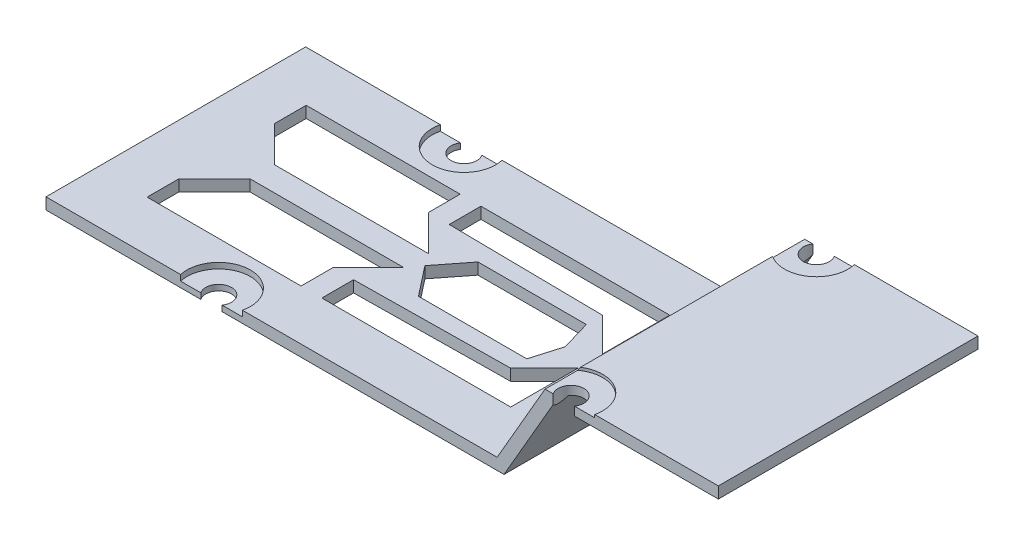
SolidWorks part; units mm, degrees
material "ABS"
ref_plane "Ön Düzlem" through (0, 0, 0) normal (0, 0, 1) x (1, 0, 0)
ref_plane "Üst Düzlem" through (0, 0, 0) normal (0, 1, 0) x (1, 0, 0)
ref_plane "Sağ Düzlem" through (0, 0, 0) normal (1, 0, 0) x (0, 0, -1)
sketch "Sketch1" plane through (0, 0, 0) normal (0, 0, 1) x (1, 0, 0)
  line L0 (-73.1543, 0) -> (-73.1543, -2)
  line L1 (44.3457, 14.9996) -> (14.3457, 14.9996)
  line L2 (14.3457, 14.9996) -> (5.6857, 0)
  line L3 (5.6857, 0) -> (-73.1543, 0)
  line L4 (-73.1543, -2) -> (6.8899, -2)
  line L5 (44.3457, 14.9996) -> (44.3457, 12.9996)
  line L6 (44.3457, 12.9996) -> (15.5499, 12.9996)
  line L7 (15.5499, 12.9996) -> (6.8899, -2)
  dimension "D1" = 120
  dimension "D2" = 17.32
  dimension "D3" = 30
  dimension "D4" = 117.5
extrude "Boss-Extrude1" add sketch "Sketch1" along normal blind 45.38
sketch "Sketch2" plane through (0, 0, 0) normal (0, 1, 0) x (1, 0, 0)
  circle A1 centre (-44.2343, -44.13) radius 2.25
ref_plane "Plane1" through (0, 0, 22.69) normal (0, 0, -1) x (-1, 0, 0)
sketch "Sketch4" plane through (0, 14.9996, 0) normal (0, 1, 0) x (1, 0, 0)
  line L0 (44.3457, -45.38) -> (17.3457, -45.38)
  line L1 (44.3457, -45.38) -> (14.3457, -45.38) construction
  line L2 (17.3457, -45.38) -> (17.3457, -44.13)
  circle A0 centre (17.3457, -44.13) radius 2.25
extrude "Cut-Extrude3" cut sketch "Sketch4" against normal up to next (14.9996 mm away) contours A0
sketch "Sketch5" plane through (0, 14.9996, 0) normal (0, 1, 0) x (1, 0, 0)
  circle A0 centre (17.3457, -44.13) radius 5.54
extrude "Cut-Extrude4" cut sketch "Sketch5" against normal blind 0.5
sketch "Sketch6" plane through (0, 0, 0) normal (0, 1, 0) x (1, 0, 0)
  line L0 (49.8222, -22.69) -> (-95.678, -22.69) construction
  line L1 (9.3498, -22.69) -> (-9.3498, -22.69) construction
  line L2 (-0.7343, -36.59) -> (-0.7343, -24.8244)
  line L3 (-33.7343, -36.59) -> (-0.7343, -36.59)
  line L4 (-0.7343, -24.8244) -> (-6.6171, -30.7072)
  line L5 (-6.6171, -30.7072) -> (-33.7343, -31.0537)
  line L6 (-33.7343, -31.0537) -> (-33.7343, -36.59)
  line L7 (-37.3689, -36.59) -> (-37.3689, -31.0537)
  line L8 (-37.3689, -31.0537) -> (-31.1395, -24.8244)
  line L9 (-31.1395, -24.8244) -> (-58.0417, -24.8244)
  line L10 (-58.0417, -24.8244) -> (-64.2711, -31.0537)
  line L11 (-64.2711, -31.0537) -> (-64.2711, -36.59)
  line L12 (-64.2711, -36.59) -> (-37.3689, -36.59)
  dimension "D1" = 33
extrude "Cut-Extrude5" cut sketch "Sketch6" against normal up to surface (2 mm away) up to face at (-33.1322, -2, 22.69)
sketch "Sketch7" plane through (0, 0, 0) normal (0, 1, 0) x (1, 0, 0)
  line L0 (-5.0958, -22.69) -> (-6.6171, -27.8905)
  line L1 (9.3498, -22.69) -> (-9.3498, -22.69) construction
  line L2 (-6.6171, -27.8905) -> (-25.5511, -27.8905)
  line L3 (-25.5511, -27.8905) -> (-29.6265, -22.69)
  line L4 (-29.6265, -22.69) -> (-5.0958, -22.69)
extrude "Cut-Extrude6" cut sketch "Sketch7" against normal up to surface (2 mm away) up to face at (-48.7435, -2, 30.8227)
extrude "Cut-Extrude7" cut sketch "Sketch2" against normal up to next (2 mm away)
sketch "Sketch8" plane through (0, 0, 0) normal (0, 1, 0) x (1, 0, 0)
  circle A0 centre (-44.2343, -44.13) radius 5.54
extrude "Cut-Extrude8" cut sketch "Sketch8" against normal blind 1
mirror "Mirror1" about plane through (0, 0, 22.69) normal (0, 0, -1) of "Cut-Extrude3", "Cut-Extrude4", "Cut-Extrude5", "Cut-Extrude6", "Cut-Extrude7", "Cut-Extrude8"
